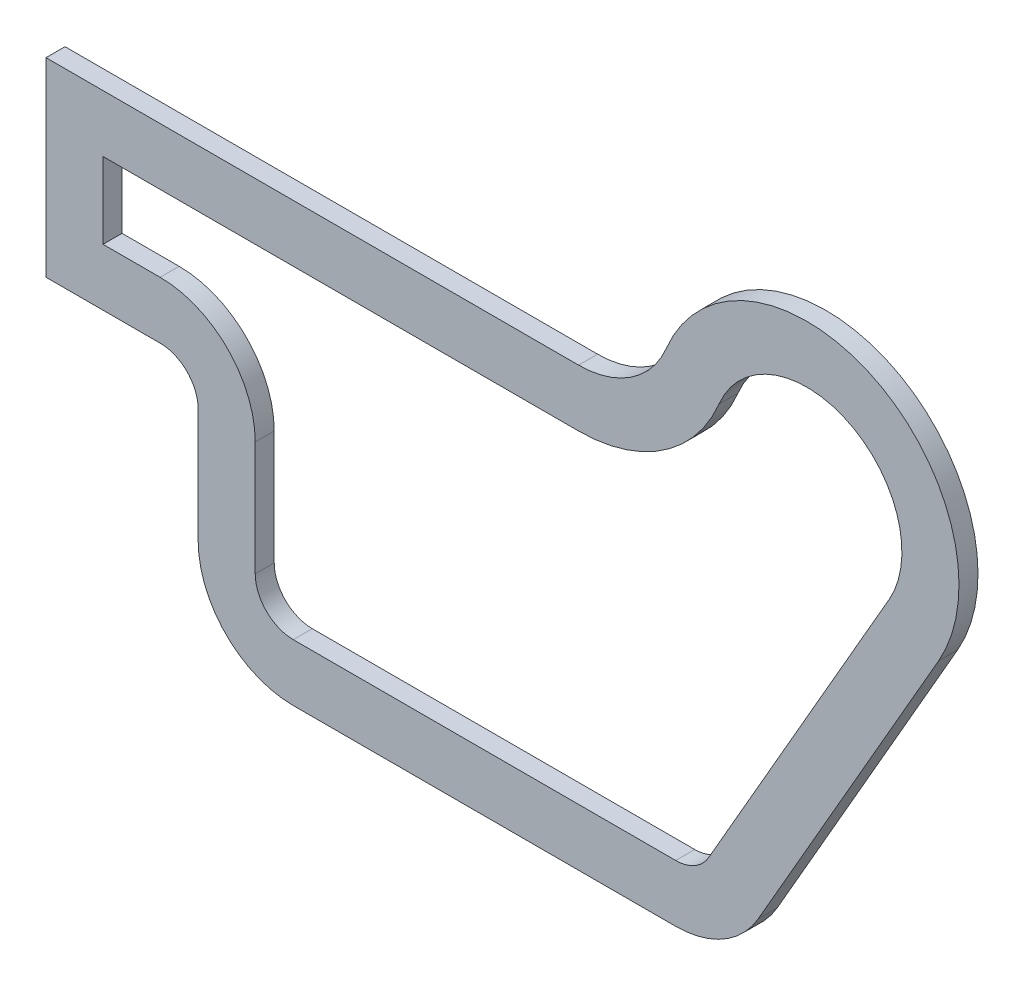
SolidWorks part; units mm, degrees
ref_plane "Front Plane" through (0, 0, 0) normal (0, 0, 1) x (1, 0, 0)
ref_plane "Top Plane" through (0, 0, 0) normal (0, 1, 0) x (1, 0, 0)
ref_plane "Right Plane" through (0, 0, 0) normal (1, 0, 0) x (0, 0, -1)
sketch "Sketch1" plane through (0, 0, 0) normal (0, 0, 1) x (1, 0, 0)
  line L0 (140, 115) -> (0, 115)
  line L1 (0, -99.8324) -> (0, 99.8324) construction
  line L2 (0, 115) -> (0, 65)
  line L3 (0, 65) -> (30, 65)
  line L4 (40, 55) -> (40, 25)
  line L5 (126.0737, 0) -> (-126.0737, 0) construction
  line L6 (234.6737, 95.0567) -> (187.21, 12.5355)
  line L7 (165.5389, 0) -> (65, 0)
  arc A0 (234.6737, 95.0567) -> (163.0769, 130.3846) centre (200, 115) ccw
  arc A1 (163.0769, 130.3846) -> (140, 115) centre (140, 140) cw
  arc A2 (40, 55) -> (30, 65) centre (30, 55) ccw
  arc A3 (65, 0) -> (40, 25) centre (65, 25) cw
  arc A4 (187.21, 12.5355) -> (165.5389, 0) centre (165.5389, 25) cw
  point P15 (160, 115)
  point P16 (0, 0)
  point P21 (40, 0)
  point P24 (180, 0)
  dimension "D1" = 50
  dimension "D6" = 80
  dimension "D7" = 25
  dimension "D8" = 10
  dimension "D9" = 25
  dimension "D10" = 25
  dimension "D2" = 200
  dimension "D3" = 40
  dimension "D4" = 180
  dimension "D5" = 115
extrude "Boss-Extrude1" add sketch "Sketch1" along normal blind 5
shell "Shell1" thickness 15
